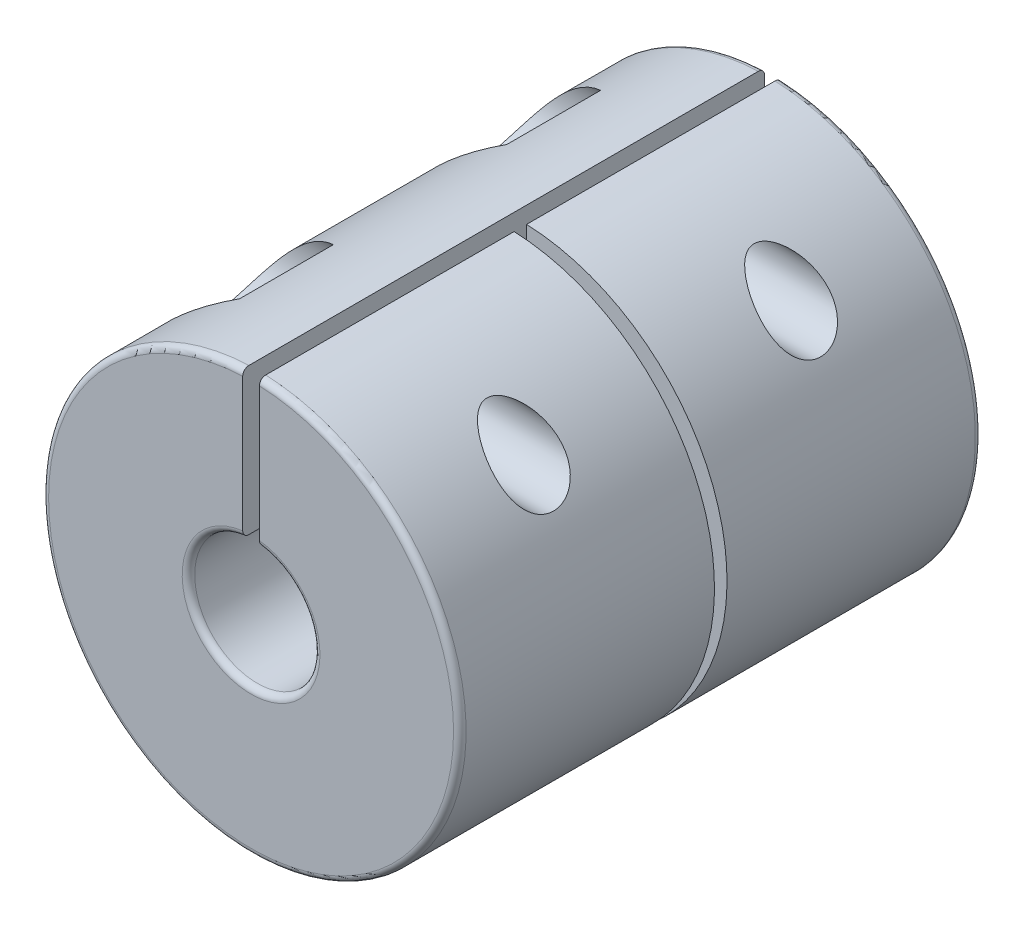
SolidWorks part; units mm, degrees
ref_plane "前视基准面" through (0, 0, 0) normal (0, 0, 1) x (1, 0, 0)
ref_plane "上视基准面" through (0, 0, 0) normal (0, 1, 0) x (1, 0, 0)
ref_plane "右视基准面" through (0, 0, 0) normal (1, 0, 0) x (0, 0, -1)
sketch "草图1" plane through (0, 0, 0) normal (0, 0, 1) x (1, 0, 0)
  circle A0 centre (0, 0) radius 10
  dimension "D1" = 20
extrude "凸台-拉伸1" add sketch "草图1" along normal mid plane 25
sketch "草图2" plane through (0, 0, 12.5) normal (0, 0, 1) x (1, 0, 0)
  circle A0 centre (0, 0) radius 3
  dimension "D1" = 6
extrude "切除-拉伸1" cut sketch "草图2" against normal through all
sketch "草图3" plane through (0, 0, -12.5) normal (0, 0, -1) x (-1, 0, 0)
  circle A0 centre (0, 0) radius 4
  dimension "D1" = 8
extrude "切除-拉伸2" cut sketch "草图3" against normal blind 12.2
sketch "草图4" plane through (0, 0, -0.3) normal (0, 0, -1) x (-1, 0, 0)
  circle A0 centre (0, 0) radius 4.5
  dimension "D1" = 9
extrude "切除-拉伸3" cut sketch "草图4" against normal blind 0.6
sketch "草图5" plane through (0, 0, 0) normal (0, 0, 1) x (1, 0, 0)
  line L1 (0.4, 12) -> (-0.4, 12)
  line L2 (0.4, 12) -> (0.4, 0)
  line L3 (0.4, 0) -> (-0.4, 0)
  line L4 (-0.4, 12) -> (-0.4, 0)
  line L5 (0.4, 12) -> (-0.4, 0) construction
  line L6 (0.4, 0) -> (-0.4, 12) construction
  point P0 (0, 6)
  point P5 (0, 0)
  dimension "D1" = 12
  dimension "D2" = 0.8
extrude "切除-拉伸4" cut sketch "草图5" against normal through all both and the other way through all
sketch "草图7" plane through (0, 0, 0) normal (0, 1, 0) x (1, 0, 0)
  line L0 (-4, 0.3) -> (4, 0.3) construction
  line L1 (10, -0.3) -> (0, -0.3)
  line L2 (10, -0.3) -> (10, 0.3)
  line L3 (10, 0.3) -> (0, 0.3)
  line L4 (0, -0.3) -> (0, 0.3)
  line L5 (10, -0.3) -> (0, 0.3) construction
  line L6 (10, 0.3) -> (0, -0.3) construction
  line L7 (4.5, -0.3) -> (-4.5, -0.3) construction
  line L8 (10, -12.5) -> (10, 12.5) construction
  point P0 (5, 0)
  point P7 (0, -0.1018)
extrude "切除-拉伸5" cut sketch "草图7" against normal through all both and the other way through all
sketch "草图8" plane through (-0.4, 0, 0) normal (1, 0, 0) x (0, 0, -1)
  line L1 (-12.5, 9.992) -> (12.5, 9.992) construction
  line L2 (12.5, 9.992) -> (12.5, 3.9799) construction
  line L3 (-12.5, 9.992) -> (-12.5, 2.9732) construction
  circle A0 centre (6.4, 6.992) radius 1.55
  circle A1 centre (-6.4, 6.992) radius 1.55
  point P4 (0, 0)
  point P5 (0, 0)
  dimension "D1" = 3.1
  dimension "D2" = 3
  dimension "D3" = 6.1
  dimension "D4" = 6.1
extrude "切除-拉伸6" cut sketch "草图8" against normal through all both and the other way through all
fillet "圆角1" radius 0.3 4 edges at (0, -4, -12.5) (0, -3, 12.5) (0, -10, -12.5) (0, -10, 12.5)
sketch "草图9" plane through (-0.4, 0, 0) normal (1, 0, 0) x (0, 0, -1)
  circle A0 centre (-6.4, 6.992) radius 3
  circle A1 centre (6.4, 6.992) radius 3
  dimension "D1" = 6
extrude "切除-拉伸7" cut sketch "草图9" against normal through all from offset 4 offset against normal yes
